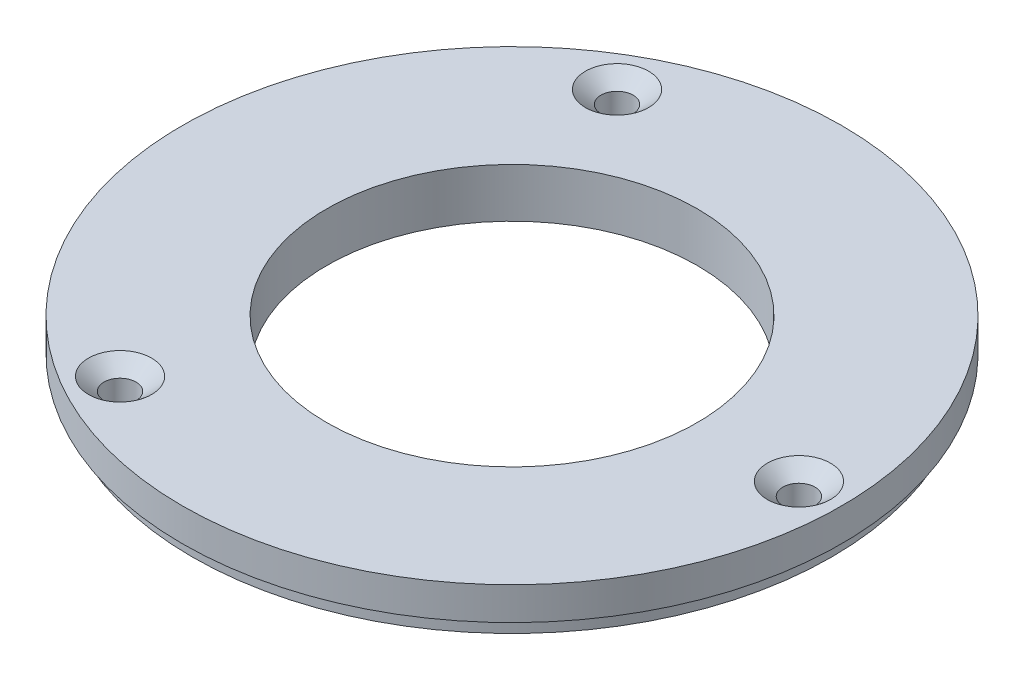
SolidWorks part; units mm, degrees
material "6061-T6 (SS)"
ref_plane "Front Plane" through (0, 0, 0) normal (0, 0, 1) x (1, 0, 0)
ref_plane "Top Plane" through (0, 0, 0) normal (0, 1, 0) x (1, 0, 0)
ref_plane "Right Plane" through (0, 0, 0) normal (1, 0, 0) x (0, 0, -1)
sketch "Sketch1" plane through (0, 0, 0) normal (0, 1, 0) x (1, 0, 0)
  circle A0 centre (0, 0) radius 51.054
  circle A1 centre (0, 0) radius 28.702
  dimension "D1" = 57.404
  dimension "D2" = 102.108
extrude "Boss-Extrude1" add sketch "Sketch1" along normal blind 7.62
hole_wizard "CSK for #10 Flat Head Machine Screw (100)1" positions "Sketch4" profile "Sketch5" countersink size "#10" standard "ANSI Inch" end condition through all
sketch "Sketch4" plane through (0, 7.62, 0) normal (0, 1, 0) x (1, 0, 0)
  line L0 (-65.4508, 0) -> (95.8403, 0) construction
  point P0 (44.45, 0)
  dimension "D1" = 44.45
sketch "Sketch5" plane through (44.45, 7.62, 0) normal (1, 0, 0) x (0, 0, 1)
  line L0 (0, 0) -> (0, 7.62)
  line L1 (0, 7.62) -> (2.4892, 7.62)
  line L2 (2.4892, 7.62) -> (2.4892, 2.0141)
  line L3 (2.4892, 2.0141) -> (4.8895, 0)
  line L5 (4.8895, 0) -> (0, 0)
  line L6 (-2.4892, 2.0141) -> (-4.8895, 0) construction
  line L11 (0, -6.35) -> (0, 107.95) construction
  dimension "Thru Hole Dia." = 4.9784
  dimension "Thru Hole Depth" = 7.62
  dimension "Near C'Sink Dia." = 9.779
  dimension "Near C'Sink Angle" = 100
pattern_circular "CirPattern1" count 4 every 120 about axis through (0, 0, 0) along (0, 1, 0) of "CSK for #10 Flat Head Machine Screw (100)1"
sketch "Sketch6" plane through (0, 0, 0) normal (0, -1, 0) x (1, 0, 0)
  circle A0 centre (0, 0) radius 49.53
  circle A1 centre (0, 0) radius 51.054
  dimension "D2" = 102.108
  dimension "D1" = 99.06
extrude "Cut-Extrude1" cut sketch "Sketch6" against normal blind 2.54
equation "\"ID\"= 2.26in"
equation "\"D1@Sketch1\"=\"ID\""
equation "\"OD\"= 4.02in"
equation "\"h\"= 0.3"
equation "\"D1@Boss-Extrude1\"=\"h\""
equation "\"HoleDist\"=1.75"
equation "\"D1@Sketch4\"=\"HoleDist\""
equation "\"D2@Sketch1\"=\"OD\""
equation "\"CouplerDia\"= 3.9"
equation "\"D1@Sketch6\"=\"CouplerDia\""
equation "\"D2@Sketch6\"=\"OD\""
